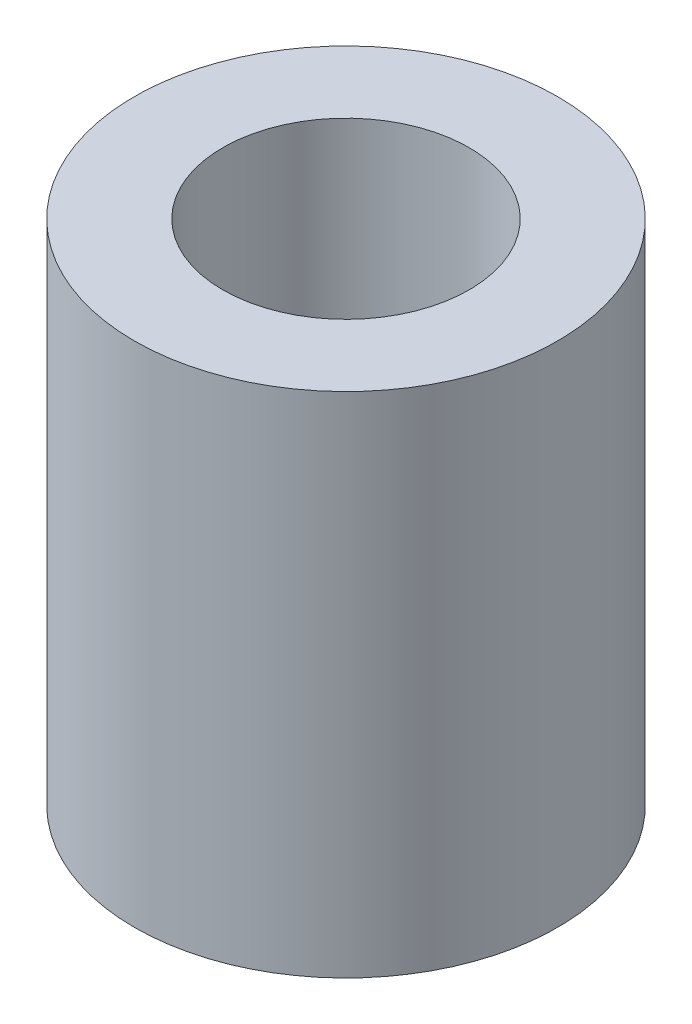
SolidWorks part; units mm, degrees
ref_plane "Front Plane" through (0, 0, 0) normal (0, 0, 1) x (1, 0, 0)
ref_plane "Top Plane" through (0, 0, 0) normal (0, 1, 0) x (1, 0, 0)
ref_plane "Right Plane" through (0, 0, 0) normal (1, 0, 0) x (0, 0, -1)
sketch "Sketch1" plane through (0, 0, 0) normal (0, 1, 0) x (1, 0, 0)
  circle A0 centre (0, 0) radius 12.5
  circle A1 centre (0, 0) radius 7.2775
  dimension "D1" = 25
extrude "Boss-Extrude1" add sketch "Sketch1" along normal blind 30
